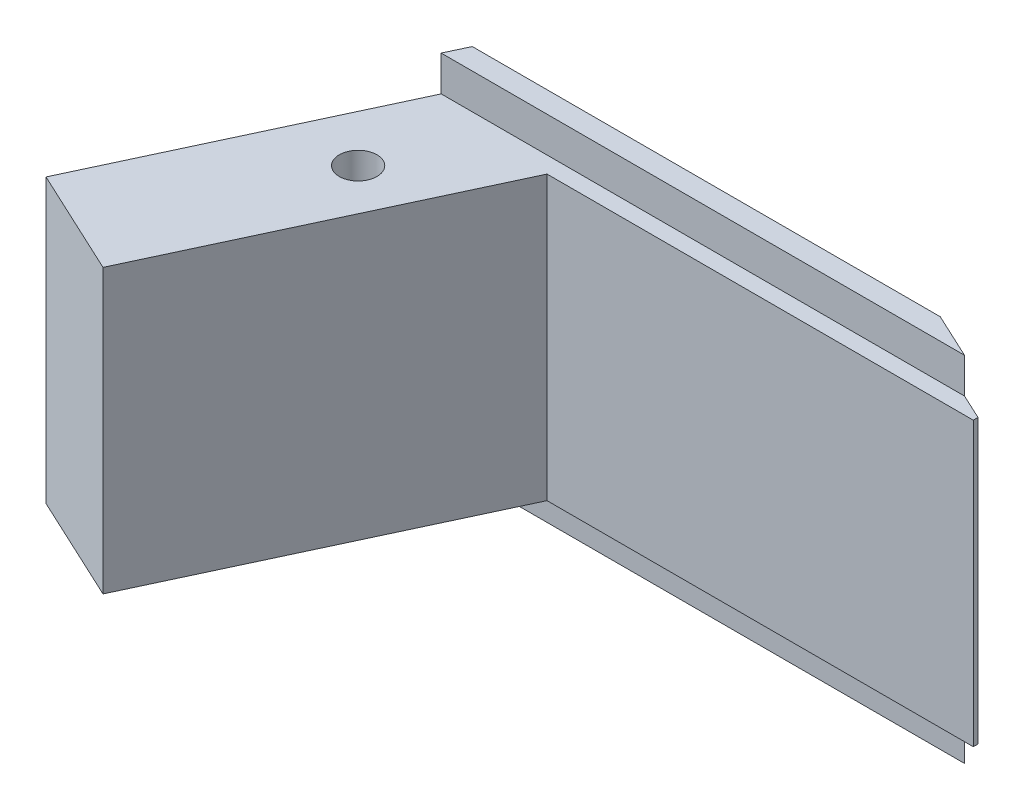
SolidWorks part; units mm, degrees
material "2024-T4"
ref_plane "Спереди" through (0, 0, 0) normal (0, 0, 1) x (1, 0, 0)
ref_plane "Сверху" through (0, 0, 0) normal (0, 1, 0) x (1, 0, 0)
ref_plane "Справа" through (0, 0, 0) normal (1, 0, 0) x (0, 0, -1)
sketch "Эскиз1" plane through (0, 0, 0) normal (0, 0, 1) x (1, 0, 0)
  line L1 (0, 0) -> (27, 0)
  line L2 (0, 0) -> (0, 15)
  line L3 (0, 15) -> (27, 15)
  line L4 (27, 0) -> (27, 15)
  dimension "D1" = 15
  dimension "D2" = 27
extrude "Бобышка-Вытянуть1" add sketch "Эскиз1" along normal blind 11
sketch "Эскиз5" plane through (0, 15, 0) normal (0, 1, 0) x (1, 0, 0)
  line L0 (27, -1.6) -> (8.9148, -1.6)
  line L1 (27, -11) -> (27, 0) construction
  line L2 (8.9148, -1.6) -> (4.5315, -11)
  line L3 (27, -11) -> (0, -11) construction
  line L4 (4.5315, -11) -> (0, -8.8869)
  line L5 (0, -11) -> (0, 0) construction
  line L6 (0, -8.8869) -> (4.144, 0)
  line L7 (27, 0) -> (0, 0) construction
  line L8 (27, -1.6) -> (27, -1.4)
  line L9 (27, -1.4) -> (23.9977, 0)
  line M1 (27, 0) -> (0, 0)
  line M2 (0, 0) -> (0, -11)
  line M3 (0, -11) -> (27, -11)
  line M4 (27, -11) -> (27, 0)
  dimension "D1" = 1.6
  dimension "D2" = 25
  dimension "D3" = 5
  dimension "D4" = 0.2
extrude "Вырез-Вытянуть6" cut sketch "Эскиз5" against normal through all contours L6 M2 M1 | L0 L2 M3 M4 | L4 M3 M2 | L9 M4 M1
sketch "Эскиз2" plane through (0, 0, 1.6) normal (0, 0, 1) x (1, 0, 0)
  line L0 (-0.8313, 13.5) -> (27.7504, 13.5)
  line L3 (-0.8313, 1.5) -> (27.7504, 1.5)
  line L5 (27, 15) -> (8.9148, 15) construction
  line L6 (-0.8313, 13.5) -> (-0.8313, 1.5)
  line L7 (27.7504, 13.5) -> (27.7504, 1.5)
  dimension "D1" = 12
  dimension "D2" = 1.5
extrude "Вырез-Вытянуть1" cut sketch "Эскиз2" against normal blind 0.7 and the other way through all flip side to cut
sketch "Эскиз3" plane through (0, 15, 0) normal (0, 1, 0) x (1, 0, 0)
  line L0 (23.7832, 0) -> (27, -1.5)
  line L1 (23.9977, 0) -> (4.144, 0) construction
  dimension "D1" = 25
extrude "Вырез-Вытянуть2" [suppressed] cut sketch "Эскиз3" against normal through all
sketch "Эскиз6" plane through (-3.4039, 0, 7.2997) normal (-0.4226, 0, 0.9063) x (0.9063, 0, 0.4226)
  line L0 (3.7558, 1.5) -> (3.7558, 13.5) construction
  line L1 (8.7558, 13.5) -> (3.7558, 13.5) construction
  line L2 (8.7558, 1.5) -> (8.7558, 13.5) construction
  line L3 (3.7558, 1.5) -> (8.7558, 1.5) construction
  line L4 (3.7558, 1.5) -> (3.7558, 13.5)
  line L5 (8.7558, 13.5) -> (3.7558, 13.5)
  line L6 (8.7558, 1.5) -> (8.7558, 13.5)
  line L7 (3.7558, 1.5) -> (8.7558, 1.5)
extrude "Бобышка-Вытянуть2" add sketch "Эскиз6" along normal offset from surface (3.8039 mm away) 22 up to face at (25.7133, 7.5, 0.8)
sketch "Эскиз7" plane through (0, 13.5, 0) normal (0, 1, 0) x (1, 0, 0)
  circle A0 centre (4.5987, -5.298) radius 0.8
  circle A1 centre (4.5987, -5.298) radius 1.3525 construction
  dimension "D1" = 1.6
extrude "Вырез-Вытянуть7" cut sketch "Эскиз7" against normal through all
